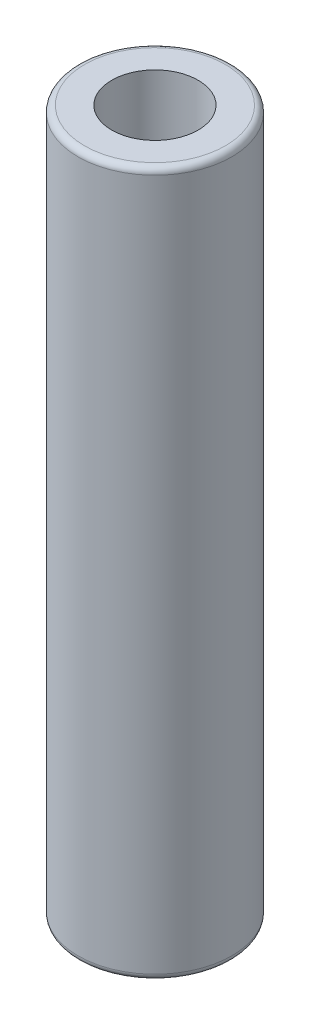
SolidWorks part; units mm, degrees
material "Chrome Stainless Steel"
ref_plane "Front" through (0, 0, 0) normal (0, 0, 1) x (1, 0, 0)
ref_plane "Top" through (0, 0, 0) normal (0, 1, 0) x (1, 0, 0)
ref_plane "Right" through (0, 0, 0) normal (1, 0, 0) x (0, 0, -1)
sketch "Sketch1" plane through (0, 0, 0) normal (0, 0, 1) x (1, 0, 0)
  line L0 (0, 288.3922) -> (0, -278.7099) construction
  line L1 (-369.3079, 0) -> (390.0556, 0) construction
  line L2 (0, 0) -> (0, 43.6753)
  line L3 (0, 43.6753) -> (8.7313, 43.6753)
  line L4 (9.525, 42.8815) -> (9.525, 0.7938)
  line L5 (9.525, 0.7938) -> (9.525, 0)
  line L6 (9.525, 0) -> (0, 0)
  arc A0 (9.525, 42.8815) -> (8.7313, 43.6753) centre (8.7313, 42.8815) ccw
  point P13 (9.525, 0)
  dimension "D3" = 0.7937
  dimension "D1" = 87.3506
  dimension "D2" = 19.05
revolve "Revolve1" add sketch "Sketch1" angle 360 about L0
hole_wizard "1/2-13 Tapped Hole1" positions "Sketch2" profile "Sketch3" tap size "1/2-13" standard "ANSI Inch"
sketch "Sketch2" plane through (0, 43.6753, 0) normal (0, 1, 0) x (1, 0, 0)
  point P0 (0, 0)
sketch "Sketch3" plane through (0, 43.6753, 0) normal (1, 0, 0) x (0, 0, 1)
  line L0 (0, 0) -> (0, 22.2695)
  line L1 (0, 22.2695) -> (5.3581, 19.05)
  line L2 (5.3581, 19.05) -> (5.3581, 0)
  line L5 (5.3581, 0) -> (0, 0)
  line L10 (0, 22.2695) -> (-5.3581, 19.05) construction
  line L11 (0, -6.35) -> (0, 107.95) construction
  dimension "Tap Drill Dia." = 10.7163
  dimension "Tap Drill Depth" = 19.05
  dimension "Drill Angle" = 118
cosmetic thread "Hole Thread1"
mirror "Mirror1" about plane through (0, 0, 0) normal (0, 1, 0) of bodies 103
